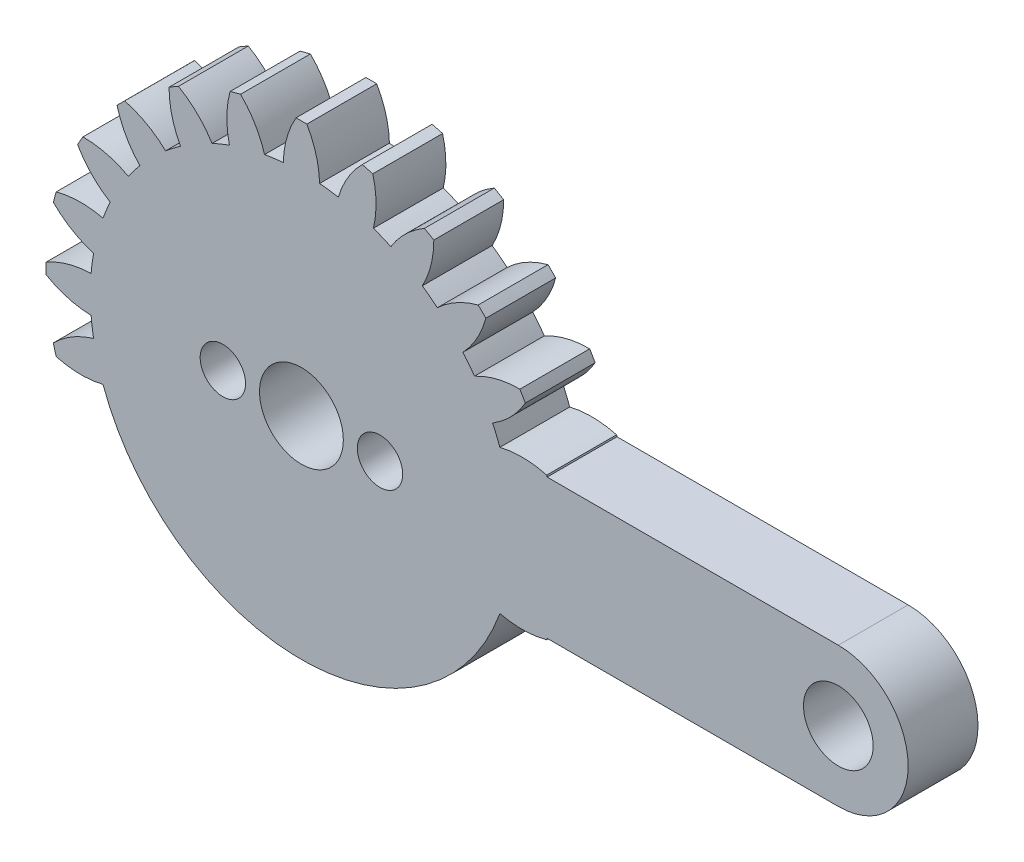
SolidWorks part; units mm, degrees
ref_plane "Front Plane" through (0, 0, 0) normal (0, 0, 1) x (1, 0, 0)
ref_plane "Top Plane" through (0, 0, 0) normal (0, 1, 0) x (1, 0, 0)
ref_plane "Right Plane" through (0, 0, 0) normal (1, 0, 0) x (0, 0, -1)
sketch "Sketch1" plane through (0, 0, 0) normal (0, 0, 1) x (1, 0, 0)
sketch "Sketch2" plane through (0, 0, 0) normal (0, 0, 1) x (1, 0, 0)
  line L0 (0, 0) -> (0, 14630) construction
  line L1 (0, 0) -> (48123.3485, 0) construction
  line L2 (11409.1235, 4000) -> (30750, 4000)
  line L3 (30750, -4000) -> (11409.1235, -4000)
  circle A0 centre (0, 0) radius 1750
  circle A1 centre (0, 0) radius 12090
  circle A2 centre (0, 0) radius 14630
  arc A3 (310, 14626.7153) -> (1040, 12045.1858) centre (-4358.3726, 11912.623) cw
  arc A4 (-310, 14626.7153) -> (-1040, 12045.1858) centre (4358.3726, 11912.623) ccw
  arc A5 (4085.1095, 14048.0881) -> (4122.0863, 11365.5842) centre (-1126.651, 12634.7401) cw
  arc A6 (3486.2355, 14208.556) -> (2112.9606, 11903.9278) centre (7293.0784, 10378.6804) ccw
  arc A7 (7581.8255, 12512.107) -> (6923.2593, 9911.4369) centre (2181.8501, 12495.8205) cw
  arc A8 (7044.8898, 12822.107) -> (5121.9265, 10951.4369) centre (9730.7729, 8137.4478) ccw
  arc A9 (10561.8527, 10123.4465) -> (9252.6236, 7781.8415) centre (5341.6617, 11505.3313) cw
  arc A10 (10123.4465, 10561.8527) -> (7781.8415, 9252.6236) centre (11505.3313, 5341.6617) ccw
  arc A11 (12822.107, 7044.8898) -> (10951.4369, 5121.9265) centre (8137.4478, 9730.7729) cw
  arc A12 (12512.107, 7581.8255) -> (9911.4369, 6923.2593) centre (12495.8205, 2181.8501) ccw
  arc A13 (14208.556, 3486.2355) -> (11903.9278, 2112.9606) centre (10378.6804, 7293.0784) cw
  arc A14 (14048.0881, 4085.1095) -> (11365.5842, 4122.0863) centre (12634.7401, -1126.651) ccw
  arc A15 (14626.7153, -310) -> (12045.1858, -1040) centre (11912.623, 4358.3726) cw
  arc A16 (14626.7153, 310) -> (12045.1858, 1040) centre (11912.623, -4358.3726) ccw
  arc A17 (14048.0881, -4085.1095) -> (11365.5842, -4122.0863) centre (12634.7401, 1126.651) cw
  arc A18 (14208.556, -3486.2355) -> (11903.9278, -2112.9606) centre (10378.6804, -7293.0784) ccw
  arc A19 (12512.107, -7581.8255) -> (9911.4369, -6923.2593) centre (12495.8205, -2181.8501) cw
  arc A20 (12822.107, -7044.8898) -> (10951.4369, -5121.9265) centre (8137.4478, -9730.7729) ccw
  arc A21 (10123.4465, -10561.8527) -> (7781.8415, -9252.6236) centre (11505.3313, -5341.6617) cw
  arc A22 (10561.8527, -10123.4465) -> (9252.6236, -7781.8415) centre (5341.6617, -11505.3313) ccw
  arc A23 (7044.8898, -12822.107) -> (5121.9265, -10951.4369) centre (9730.7729, -8137.4478) cw
  arc A24 (7581.8255, -12512.107) -> (6923.2593, -9911.4369) centre (2181.8501, -12495.8205) ccw
  arc A25 (3486.2355, -14208.556) -> (2112.9606, -11903.9278) centre (7293.0784, -10378.6804) cw
  arc A26 (4085.1095, -14048.0881) -> (4122.0863, -11365.5842) centre (-1126.651, -12634.7401) ccw
  arc A27 (-310, -14626.7153) -> (-1040, -12045.1858) centre (4358.3726, -11912.623) cw
  arc A28 (310, -14626.7153) -> (1040, -12045.1858) centre (-4358.3726, -11912.623) ccw
  arc A29 (-4085.1095, -14048.0881) -> (-4122.0863, -11365.5842) centre (1126.651, -12634.7401) cw
  arc A30 (-3486.2355, -14208.556) -> (-2112.9606, -11903.9278) centre (-7293.0784, -10378.6804) ccw
  arc A31 (-7581.8255, -12512.107) -> (-6923.2593, -9911.4369) centre (-2181.8501, -12495.8205) cw
  arc A32 (-7044.8898, -12822.107) -> (-5121.9265, -10951.4369) centre (-9730.7729, -8137.4478) ccw
  arc A33 (-10561.8527, -10123.4465) -> (-9252.6236, -7781.8415) centre (-5341.6617, -11505.3313) cw
  arc A34 (-10123.4465, -10561.8527) -> (-7781.8415, -9252.6236) centre (-11505.3313, -5341.6617) ccw
  arc A35 (-12822.107, -7044.8898) -> (-10951.4369, -5121.9265) centre (-8137.4478, -9730.7729) cw
  arc A36 (-12512.107, -7581.8255) -> (-9911.4369, -6923.2593) centre (-12495.8205, -2181.8501) ccw
  arc A37 (-14208.556, -3486.2355) -> (-11903.9278, -2112.9606) centre (-10378.6804, -7293.0784) cw
  arc A38 (-14048.0881, -4085.1095) -> (-11365.5842, -4122.0863) centre (-12634.7401, 1126.651) ccw
  arc A39 (-14626.7153, 310) -> (-12045.1858, 1040) centre (-11912.623, -4358.3726) cw
  arc A40 (-14626.7153, -310) -> (-12045.1858, -1040) centre (-11912.623, 4358.3726) ccw
  arc A41 (-14048.0881, 4085.1095) -> (-11365.5842, 4122.0863) centre (-12634.7401, -1126.651) cw
  arc A42 (-14208.556, 3486.2355) -> (-11903.9278, 2112.9606) centre (-10378.6804, 7293.0784) ccw
  arc A43 (-12512.107, 7581.8255) -> (-9911.4369, 6923.2593) centre (-12495.8205, 2181.8501) cw
  arc A44 (-12822.107, 7044.8898) -> (-10951.4369, 5121.9265) centre (-8137.4478, 9730.7729) ccw
  arc A45 (-10123.4465, 10561.8527) -> (-7781.8415, 9252.6236) centre (-11505.3313, 5341.6617) cw
  arc A46 (-10561.8527, 10123.4465) -> (-9252.6236, 7781.8415) centre (-5341.6617, 11505.3313) ccw
  arc A47 (-7044.8898, 12822.107) -> (-5121.9265, 10951.4369) centre (-9730.7729, 8137.4478) cw
  arc A48 (-7581.8255, 12512.107) -> (-6923.2593, 9911.4369) centre (-2181.8501, 12495.8205) ccw
  arc A49 (-3486.2355, 14208.556) -> (-2112.9606, 11903.9278) centre (-7293.0784, 10378.6804) cw
  arc A50 (-4085.1095, 14048.0881) -> (-4122.0863, 11365.5842) centre (1126.651, 12634.7401) ccw
  arc A51 (30750, 4000) -> (30750, -4000) centre (30750, 0) cw
  circle A52 centre (30750, 0) radius 1995
  point P153 (0, 0)
  dimension "D1" = 3500
  dimension "D2" = 24180
  dimension "D3" = 24180
  dimension "D4" = 29260
  dimension "D7" = 5400
  dimension "D9" = 4000
  dimension "D10" = 3990
  dimension "D5" = 620
  dimension "D6" = 2080
  dimension "D8" = 30750
  dimension "D11" = 24
extrude "Boss-Extrude1" add sketch "Sketch2" along normal blind 4000 contours A51 L2 A2 L3 A52 | A1 | A13 A2 L2 A1 | A2 A14 A1 L2 | A2 A16 A1 A15 | A16 A2 A13 A1 | A18 A2 A15 A1 | A2 A18 A1 L3 | A17 A2 L3 A1 | A2 A12 A1 A11 | A2 A10 A1 A9 | A2 A8 A1 A7 | A2 A6 A1 A5 | A2 A4 A1 A3 | A2 A50 A1 A49 | A2 A48 A1 A47 | A2 A46 A1 A45 | A2 A44 A1 A43 | A2 A42 A1 A41 | A2 A40 A1 A39 | A2 A38 A1 A37
sketch "Sketch3" plane through (0, 0, 4000) normal (0, 0, 1) x (1, 0, 0)
  line L0 (-4500, 0) -> (4500, 0) construction
  circle A0 centre (4500, 0) radius 1300
  circle A1 centre (-4500, 0) radius 1300
  circle A2 centre (0, 0) radius 2400
  dimension "D3" = 2600
  dimension "D4" = 4800
  dimension "D1" = 9000
  dimension "D2" = 4500
extrude "Cut-Extrude1" cut sketch "Sketch3" against normal through all
